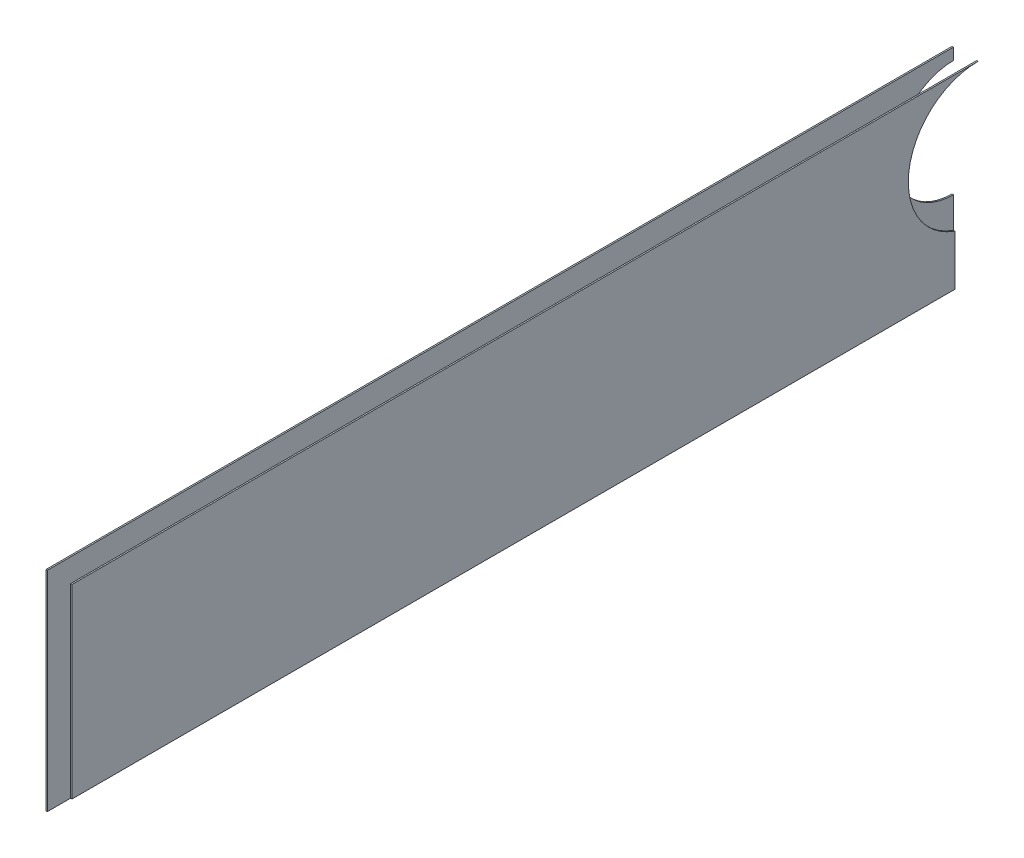
SolidWorks part; units mm, degrees
material "Thornel Mat VMA"
ref_plane "Płaszczyzna XY" through (0, 0, 0) normal (0, 0, 1) x (1, 0, 0)
ref_plane "Płaszczyzna XZ" through (0, 0, 0) normal (0, 1, 0) x (1, 0, 0)
ref_plane "Płaszczyzna YZ" through (0, 0, 0) normal (1, 0, 0) x (0, 0, -1)
sketch "Szkic1" plane through (-516.203, 0, 0) normal (1, 0, 0) x (0, 0, -1)
  line L4 (-432.6816, 705) -> (-242.6816, 705)
  line L5 (-242.6816, 705) -> (-242.6816, 715.8579)
  line L6 (-237.6816, 745) -> (-432.6816, 745)
  line L7 (-432.6816, 745) -> (-432.6816, 705)
  line L8 (-432.6816, 705) -> (-242.6816, 705)
  line L9 (-242.6816, 705) -> (-242.6816, 715.8579)
  line L10 (-237.6816, 745) -> (-432.6816, 745)
  line L11 (-432.6816, 745) -> (-432.6816, 705)
  arc A1 (-237.6816, 745) -> (-242.6816, 715.8579) centre (-237.6816, 730) ccw
  arc A2 (-237.6816, 745) -> (-242.6816, 715.8579) centre (-237.6816, 730) ccw
  dimension "D1" = 0
extrude "Dodanie-wyciągnięcie1" add sketch "Szkic1" along normal blind 0.3
sketch "Szkic2" plane through (-521.203, 0, 0) normal (-1, 0, 0) x (0, 0, 1)
  line L5 (432.6816, 700) -> (432.6816, 745)
  line L6 (432.6816, 745) -> (237.6816, 745)
  line L7 (237.6816, 745) -> (237.6816, 742.5)
  line L8 (237.6816, 717.5) -> (237.6816, 700)
  line L9 (237.6816, 700) -> (432.6816, 700)
  line L10 (432.6816, 700) -> (432.6816, 745)
  line L11 (432.6816, 745) -> (237.6816, 745)
  line L12 (237.6816, 745) -> (237.6816, 742.5)
  line L13 (237.6816, 717.5) -> (237.6816, 700)
  line L14 (237.6816, 700) -> (432.6816, 700)
  arc A1 (237.6816, 717.5) -> (237.6816, 742.5) centre (237.6816, 730) ccw
  arc A2 (237.6816, 717.5) -> (237.6816, 742.5) centre (237.6816, 730) ccw
  dimension "D1" = 0
extrude "Dodanie-wyciągnięcie2" add sketch "Szkic2" along normal blind 0.3 separate body
